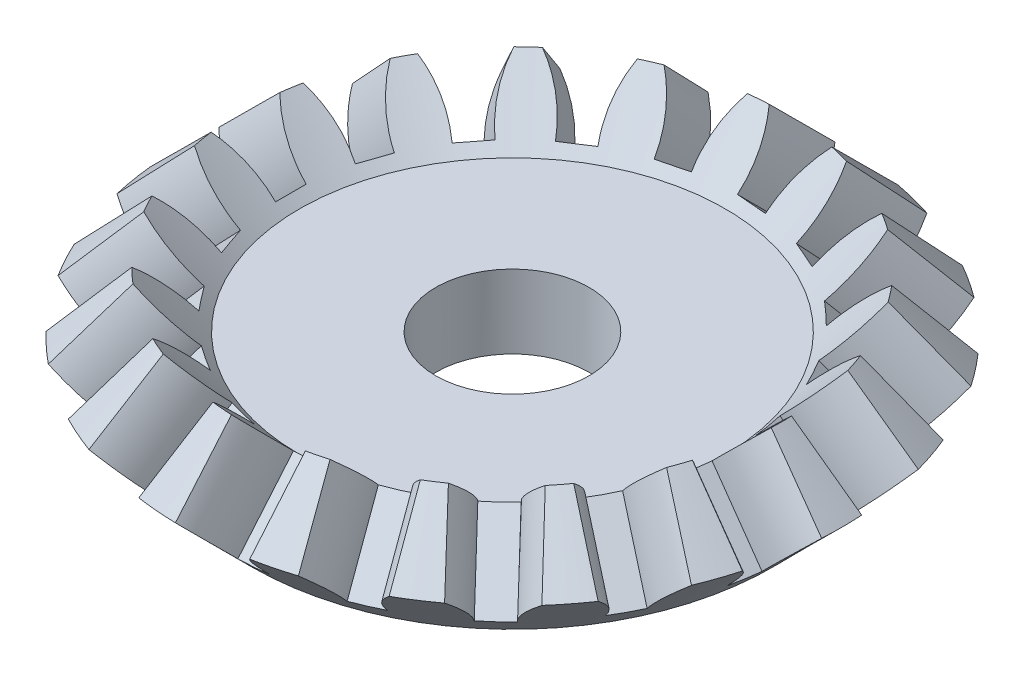
SolidWorks part; units mm, degrees
ref_plane "Front" through (0, 0, 0) normal (0, 0, 1) x (1, 0, 0)
ref_plane "Top" through (0, 0, 0) normal (0, 1, 0) x (1, 0, 0)
ref_plane "Right" through (0, 0, 0) normal (1, 0, 0) x (0, 0, -1)
sketch "Sketch2" plane through (0, 0, 0) normal (1, 0, 0) x (0, 0, -1)
  line L0 (0, 0) -> (-19.7455, 0)
  line L1 (-19.7455, 0) -> (-24.9922, 5.2467)
  line L2 (-24.9922, 5.2467) -> (-20.3929, 9.846)
  line L3 (-20.3929, 9.846) -> (-16.1221, 5.5752)
  line L4 (-16.1221, 5.5752) -> (0, 5.5752)
  line L5 (0, 55) -> (0, -55) construction
  line L6 (0, 5.5752) -> (0, 0)
  dimension "D1" = 19.7455
  dimension "D2" = 6.5044
  dimension "D3" = 6.0398
  dimension "D4" = 5.5752
  dimension "D5" = 45
revolve "Revolve2" add sketch "Sketch2" angle 360 about L6
sketch "Sketch3" plane through (0, 0, 0) normal (0, 0, 1) x (1, 0, 0)
  line L0 (0, 30.2389) -> (0, -7.011) construction
  line L1 (0, 30.2389) -> (-31.7272, -1.4884) construction
  line L2 (-20.3929, 9.846) -> (-24.9922, 5.2467) construction
ref_plane "Plane1" through (-9.8727, -9.8727, 0) normal (-0.7071, -0.7071, 0) x (0, 0, 1)
sketch "Sketch4" plane through (-9.8727, -9.8727, 0) normal (-0.7071, -0.7071, 0) x (0, 0, 1)
  line L0 (-1.1615, 16.3054) -> (1.1615, 16.3054)
  line L1 (0, 21.3821) -> (0, -4.9575) construction
  line L2 (3.7168, 22.7052) -> (-3.7168, 22.7052)
  line L3 (0, 24.746) -> (0, 11.4508) construction
  arc A0 (1.1615, 16.3054) -> (3.7168, 22.7052) centre (10.4535, 16.3054) cw
  arc A1 (-1.1615, 16.3054) -> (-3.7168, 22.7052) centre (-10.4535, 16.3054) ccw
  point P9 (0, 16.3054)
  point P12 (0, 22.7052)
  dimension "D2" = 9.292
  dimension "D1" = 1.1615
  dimension "D3" = 3.7168
extrude "Cut-Extrude1" cut sketch "Sketch4" against normal up to next
pattern_circular "CirPattern3" count 19 over 360 about axis through (0, 0, 0) along (0, 1, 0) of "Cut-Extrude1"
sketch "Sketch5" plane through (0, 5.5752, 0) normal (0, 1, 0) x (1, 0, 0)
  circle A0 centre (0, 0) radius 5.8075
  dimension "D1" = 11.615
extrude "Cut-Extrude2" cut sketch "Sketch5" against normal up to next
